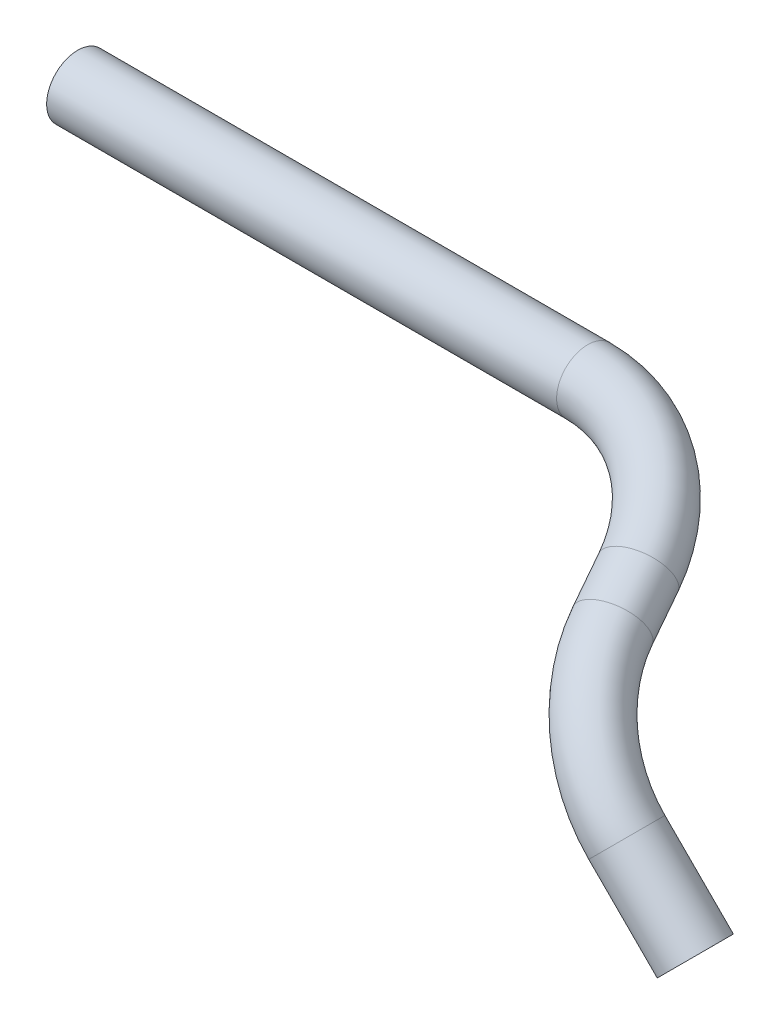
SolidWorks part; units mm, degrees
material "1060 Alloy"
ref_plane "Front Plane" through (0, 0, 0) normal (0, 0, 1) x (1, 0, 0)
ref_plane "Top Plane" through (0, 0, 0) normal (0, 1, 0) x (1, 0, 0)
ref_plane "Right Plane" through (0, 0, 0) normal (1, 0, 0) x (0, 0, -1)
sketch3d "3DSketch1"
  line L0 (0, 0, 0) -> (38.1845, -38.1845, 0) construction
  line L1 (0, 0, 0) -> (35.8649, 0, 0) construction
  line L2 (0, 0, 0) -> (-27.9578, 27.9578, 0)
  line L3 (-65.4486, 68.2382, -31.6887) -> (-71.4853, 75.7309, -48.2267)
  line L4 (-131.742, 93.668, -87.8182) -> (-339.9371, 93.668, -87.8182)
  arc A0 (-71.4853, 75.7309, -48.2267) -> (-131.742, 93.668, -87.8182) centre (-131.742, 67.463, -29.9775) ccw
  arc A1 (-27.9578, 27.9578, 0) -> (-65.4486, 68.2382, -31.6887) centre (-25.1681, 30.7474, -63.3773) ccw
  point P11 (-85.9371, 93.668, -87.8182)
  point P12 (-131.742, 125.3037, -3.7725)
  point P15 (-53.8815, 53.8815, 0)
  point P16 (-69.9827, -14.0671, -67.3225)
  dimension "D5" = 63.5
  dimension "D1" = 45
  dimension "D2" = 76.2
  dimension "D3" = 101.6
  dimension "D4" = 254
  dimension "D6" = 120
sweep "Sweep1" add path "3DSketch1" circular profile diameter 25.4 parameters "D3"=25.4
